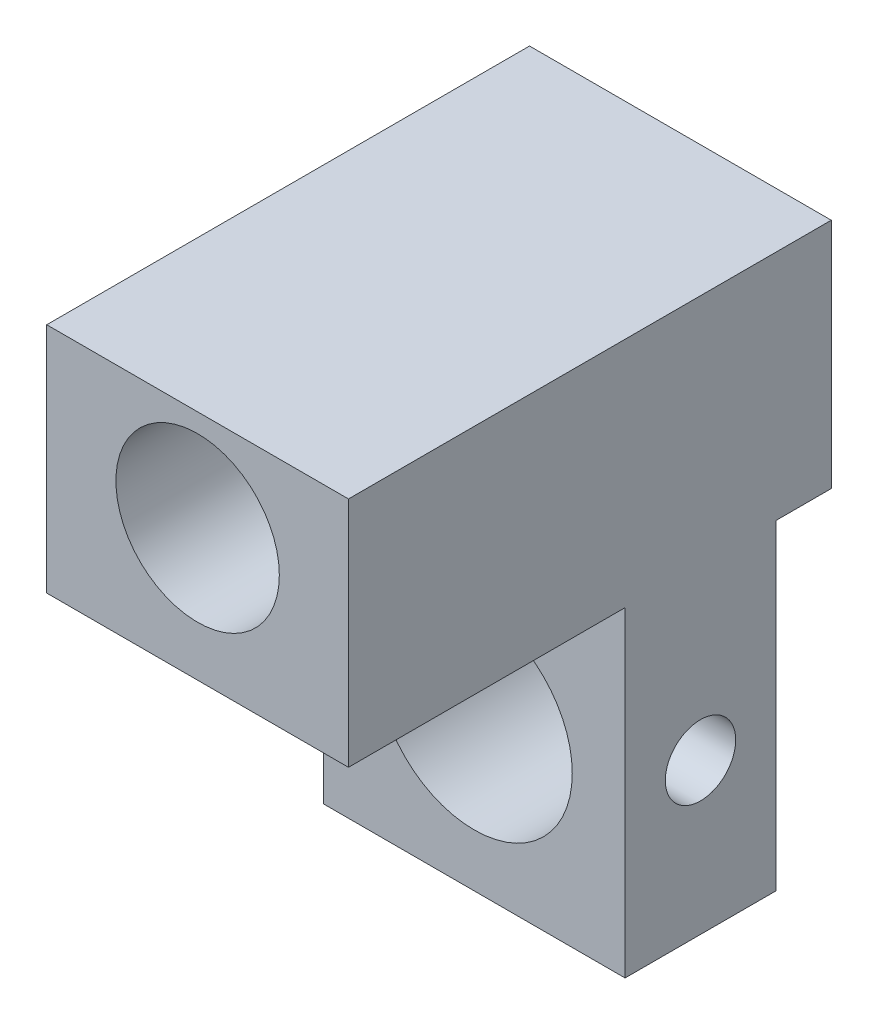
SolidWorks part; units mm, degrees
ref_plane "Plan de face" through (0, 0, 0) normal (0, 0, 1) x (1, 0, 0)
ref_plane "Plan de dessus" through (0, 0, 0) normal (0, 1, 0) x (1, 0, 0)
ref_plane "Plan de droite" through (0, 0, 0) normal (1, 0, 0) x (0, 0, -1)
sketch "Esquisse1" plane through (0, 0, 0) normal (0, 0, 1) x (1, 0, 0)
  line L0 (0, 12) -> (0, -12) construction
  line L1 (-6, -12) -> (6, -12)
  line L2 (-6, -12) -> (-6, 12)
  line L3 (-6, 12) -> (6, 12)
  line L4 (6, -12) -> (6, 12)
  line L5 (-6, -12) -> (6, 12) construction
  line L6 (-6, 12) -> (6, -12) construction
  point P0 (0, 0)
  dimension "D1" = 24
  dimension "D2" = 12
extrude "Boss.-Extru.1" add sketch "Esquisse1" along normal blind 6
sketch "Esquisse2" plane through (0, 0, 6) normal (0, 0, 1) x (1, 0, 0)
  line L0 (-6, 0) -> (6, 0) construction
  line L1 (-6, 12) -> (-6, -12) construction
  line L2 (6, -12) -> (6, 12) construction
  line L3 (0, 0) -> (0, -12) construction
  line L4 (-6, -12) -> (6, -12) construction
  circle A0 centre (0, -6) radius 3.9
sketch "Esquisse3" plane through (0, 0, 6) normal (0, 0, 1) x (1, 0, 0)
  line L0 (-6, 0) -> (6, 0) construction
  line L1 (-6, 12) -> (-6, -12) construction
  line L2 (6, -12) -> (6, 12) construction
  line L3 (0, 0) -> (0, 12) construction
  line L4 (6, 12) -> (-6, 12) construction
  circle A0 centre (0, 6) radius 3.25
extrude "Enlèv. mat.-Extru.1" cut sketch "Esquisse3" against normal blind 10
sketch "Esquisse11" plane through (0, 0, 0) normal (0, 0, -1) x (-1, 0, 0)
  line L0 (6, 0.7565) -> (-6, 0.7565) construction
  line L4 (6, 12) -> (-6, 12)
  line L5 (6, 12) -> (6, 0.7565)
  line L6 (6, 0.7565) -> (-6, 0.7565)
  line L7 (-6, 12) -> (-6, 0.7565)
  circle A0 centre (0, 6) radius 3.25
sketch "Esquisse4" plane through (0, 0, 6) normal (0, 0, 1) x (1, 0, 0)
  circle A0 centre (0, 6) radius 3.25
  circle A1 centre (0, 6) radius 5
extrude "Enlèv. mat.-Extru.2" cut sketch "Esquisse2" against normal blind 10
sketch "Esquisse5" plane through (6, 0, 0) normal (1, 0, 0) x (0, 0, -1)
  line L0 (-6, 0) -> (0, 0) construction
  line L1 (-6, -12) -> (-6, 12) construction
  line L2 (0, -12) -> (0, 12) construction
  line L3 (-3, -12) -> (-3, 0) construction
  line L4 (-6, -12) -> (0, -12) construction
  circle A0 centre (-3, -6) radius 1.4
extrude "Enlèv. mat.-Extru.3" cut sketch "Esquisse5" against normal blind 22
sketch "Esquisse6" plane through (0, 0, 0) normal (0, 0, -1) x (-1, 0, 0)
  circle A0 centre (0, 6) radius 3.25
  circle A1 centre (0, 6) radius 4.5
extrude "Boss.-Extru.4" add sketch "Esquisse6" along normal blind 0.1
sketch "Esquisse7" plane through (0, 0, 0) normal (1, 0, 0) x (0, 0, -1)
  line L0 (0.1, 10.5) -> (0.1, 1.5) construction
  line L1 (0.1, 6) -> (0.1, 10.5) construction
  line L2 (0.1, 6) -> (17.9067, 6) construction
  line L3 (0.1, 10.5) -> (0.1, 9.25)
  line L4 (3.35, 6) -> (4.6, 6)
  arc A0 (0.1, 10.5) -> (4.6, 6) centre (0.1, 6) cw
  arc A1 (0.1, 9.25) -> (3.35, 6) centre (0.1, 6) cw
revolve "Révolution1" add sketch "Esquisse7" angle 360 about L2
sketch "Esquisse8" plane through (6, 0, 0) normal (1, 0, 0) x (0, 0, -1)
  line L0 (0.1, 10.5) -> (0.1, 1.5) construction
  line L1 (2.2, 12.2518) -> (23.4237, 12.2518)
  line L2 (2.2, 12.2518) -> (2.2, 0.1384)
  line L3 (2.2, 0.1384) -> (23.4237, 0.1384)
  line L4 (23.4237, 12.2518) -> (23.4237, 0.1384)
  arc A0 (0.1, 1.5) -> (0.1, 10.5) centre (0.1, 6) ccw construction
  dimension "D1" = 2.1
extrude "Enlèv. mat.-Extru.4" cut sketch "Esquisse8" against normal blind 19
sketch "Esquisse9" plane through (6, 0, 0) normal (1, 0, 0) x (0, 0, -1)
  line L0 (-6, 0) -> (0, 0) construction
  line L1 (-6, -12) -> (-6, 12) construction
  line L2 (0, -12) -> (0, 12) construction
  line L3 (-3, 0) -> (-3, 12) construction
  line L4 (-6, 12) -> (0, 12) construction
  circle A0 centre (-3, 6) radius 1.625
extrude "Enlèv. mat.-Extru.5" cut sketch "Esquisse9" against normal blind 19
extrude "Boss.-Extru.5" add sketch "Esquisse4" along normal blind 11
extrude "Boss.-Extru.6" add sketch "Esquisse11" along normal blind 2.2 and the other way blind 17
sketch "Esquisse12" plane through (-6, 0, 0) normal (-1, 0, 0) x (0, 0, 1)
  line L0 (17, 0.7565) -> (17, 12) construction
  line L1 (-4.1, 12) -> (17, 12)
  line L2 (-4.1, 12) -> (-4.1, 10)
  line L3 (-4.1, 10) -> (17, 10)
  line L4 (17, 12) -> (17, 10)
  dimension "D1" = 2
extrude "Enlèv. mat.-Extru.6" cut sketch "Esquisse12" against normal blind 13.1
